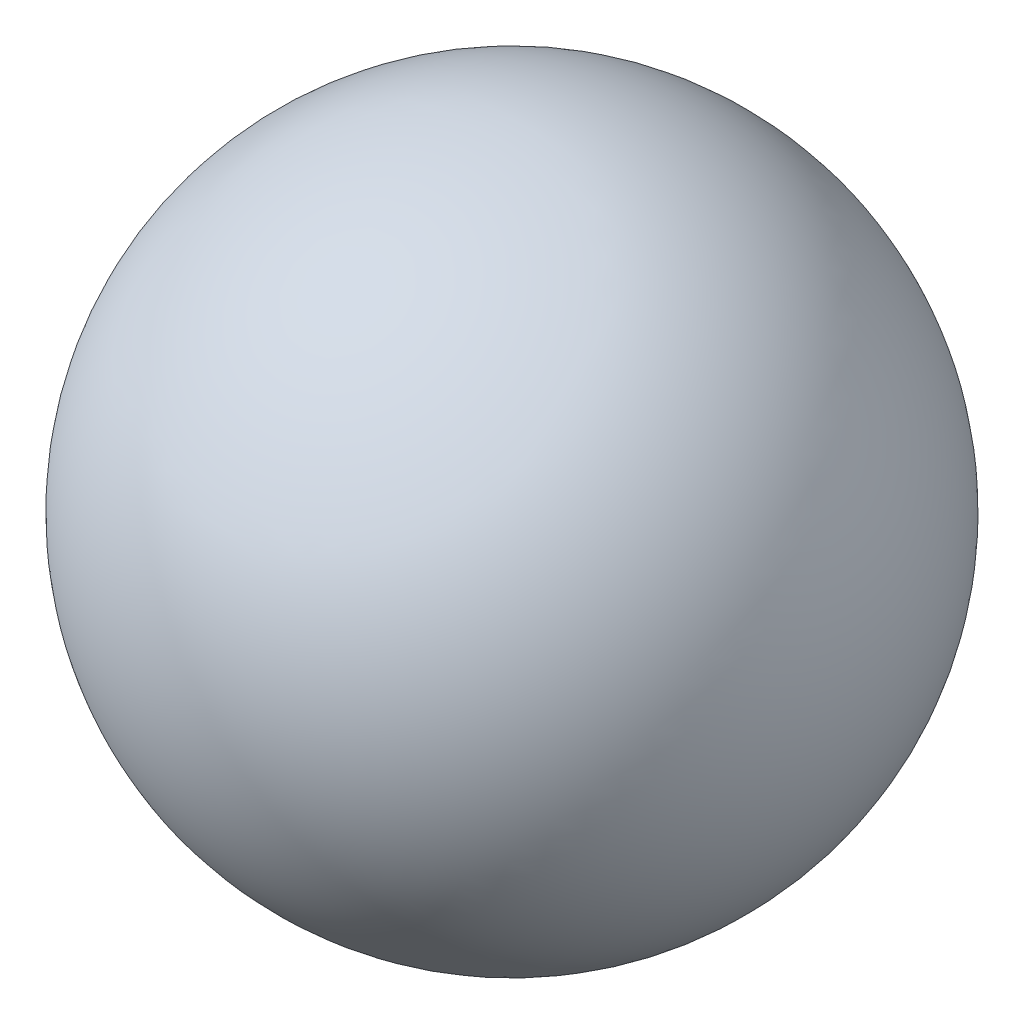
SolidWorks part; units mm, degrees
material "PEI"
ref_plane "Front Plane" through (0, 0, 0) normal (0, 0, 1) x (1, 0, 0)
ref_plane "Top Plane" through (0, 0, 0) normal (0, 1, 0) x (1, 0, 0)
ref_plane "Right Plane" through (0, 0, 0) normal (1, 0, 0) x (0, 0, -1)
sketch "Sketch1" plane through (0, 0, 0) normal (0, 1, 0) x (1, 0, 0)
  line L0 (0, 20) -> (0, -20) construction
  line L1 (0, 20) -> (0, -20)
  arc A0 (0, 20) -> (0, -20) centre (0, 0) ccw
  dimension "D1" = 40
revolve "Revolve3" add sketch "Sketch1" angle 360 about L0
